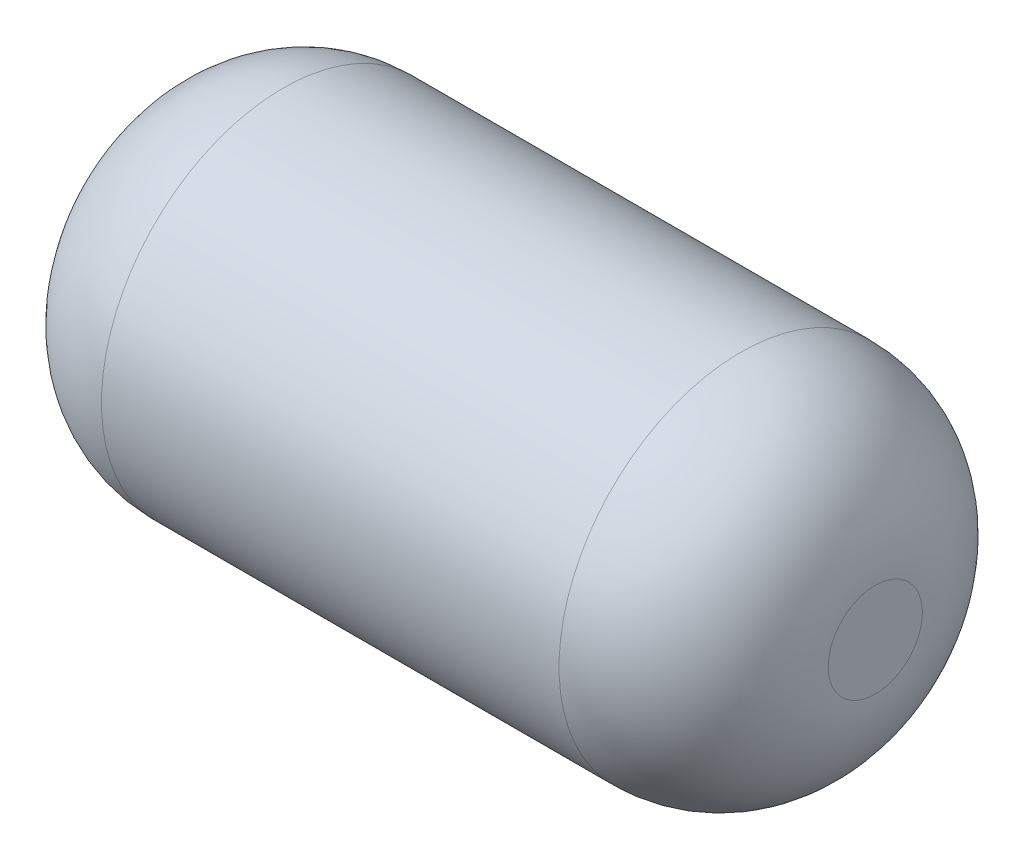
SolidWorks part; units mm, degrees
ref_plane "Front Plane" through (0, 0, 0) normal (0, 0, 1) x (1, 0, 0)
ref_plane "Top Plane" through (0, 0, 0) normal (0, 1, 0) x (1, 0, 0)
ref_plane "Right Plane" through (0, 0, 0) normal (1, 0, 0) x (0, 0, -1)
sketch "Sketch1" plane through (0, 0, 0) normal (1, 0, 0) x (0, 0, -1)
  circle A0 centre (0, 0) radius 67.5
  dimension "D1" = 135
extrude "Boss-Extrude1" add sketch "Sketch1" along normal mid plane 270
fillet "Fillet1" radius 50 2 edges at (135, 0, -67.5) (-135, 0, -67.5)
